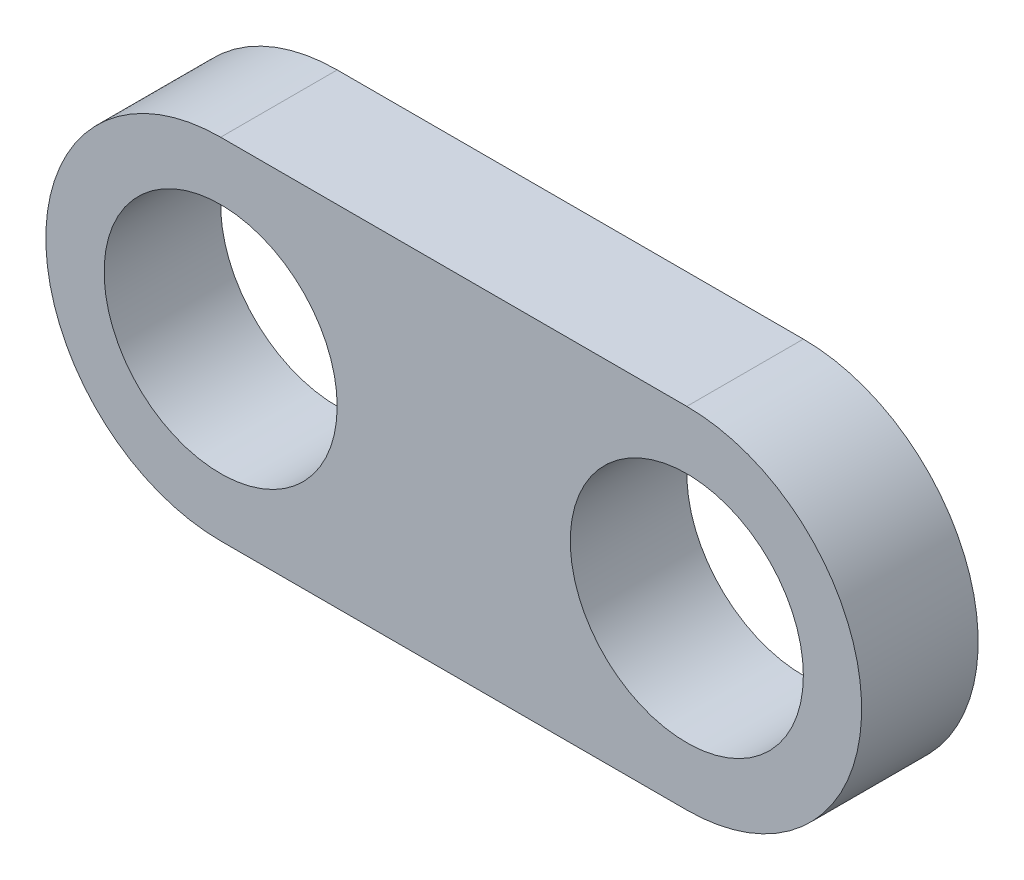
SolidWorks part; units mm, degrees
ref_plane "Front Plane" through (0, 0, 0) normal (0, 0, 1) x (1, 0, 0)
ref_plane "Top Plane" through (0, 0, 0) normal (0, 1, 0) x (1, 0, 0)
ref_plane "Right Plane" through (0, 0, 0) normal (1, 0, 0) x (0, 0, -1)
sketch "Sketch1" plane through (0, 0, 0) normal (0, 0, 1) x (1, 0, 0)
  line L0 (0, 0) -> (40, 0) construction
  line L1 (0, 15) -> (40, 15)
  line L2 (40, -15) -> (0, -15)
  circle A0 centre (0, 0) radius 10
  circle A1 centre (40, 0) radius 10
  arc A2 (0, 15) -> (0, -15) centre (0, 0) ccw
  arc A3 (40, -15) -> (40, 15) centre (40, 0) ccw
  dimension "D1" = 20
  dimension "D2" = 20
  dimension "D3" = 30
  dimension "D4" = 30
  dimension "D5" = 40
extrude "Boss-Extrude1" add sketch "Sketch1" along normal blind 10
